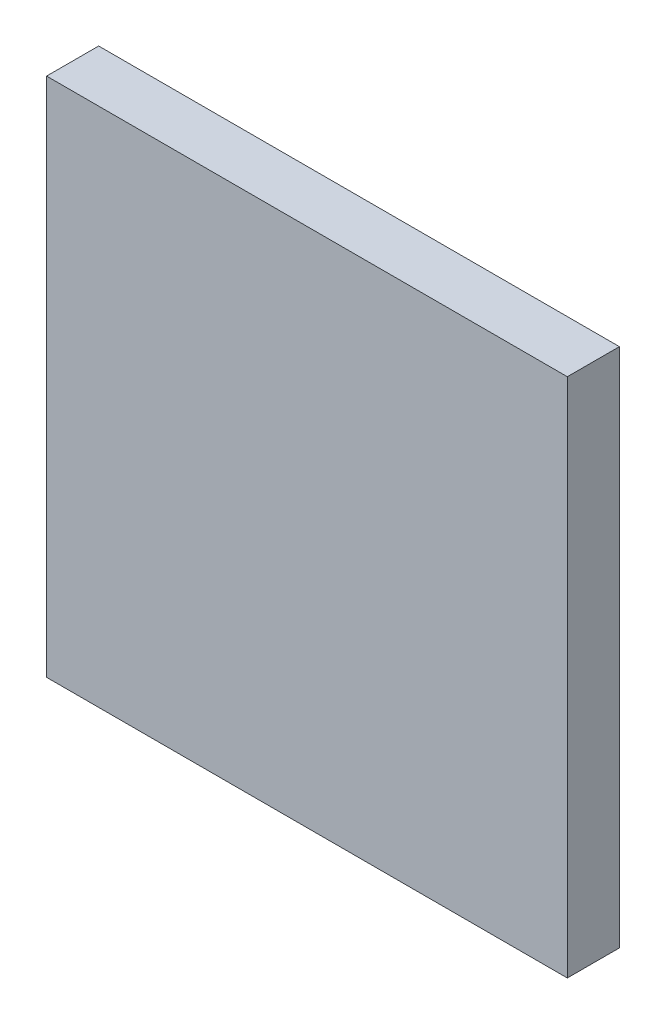
SolidWorks part; units mm, degrees
material "Mahogany"
ref_plane "Front Plane" through (0, 0, 0) normal (0, 0, 1) x (1, 0, 0)
ref_plane "Top Plane" through (0, 0, 0) normal (0, 1, 0) x (1, 0, 0)
ref_plane "Right Plane" through (0, 0, 0) normal (1, 0, 0) x (0, 0, -1)
sketch "Sketch1" plane through (0, 0, 0) normal (0, 0, 1) x (1, 0, 0)
  line L1 (0, 0) -> (-508, 0)
  line L2 (0, 0) -> (0, 508)
  line L3 (0, 508) -> (-508, 508)
  line L4 (-508, 0) -> (-508, 508)
  dimension "D1" = 508
  dimension "D2" = 508
extrude "Boss-Extrude1" add sketch "Sketch1" along normal blind 50.8
